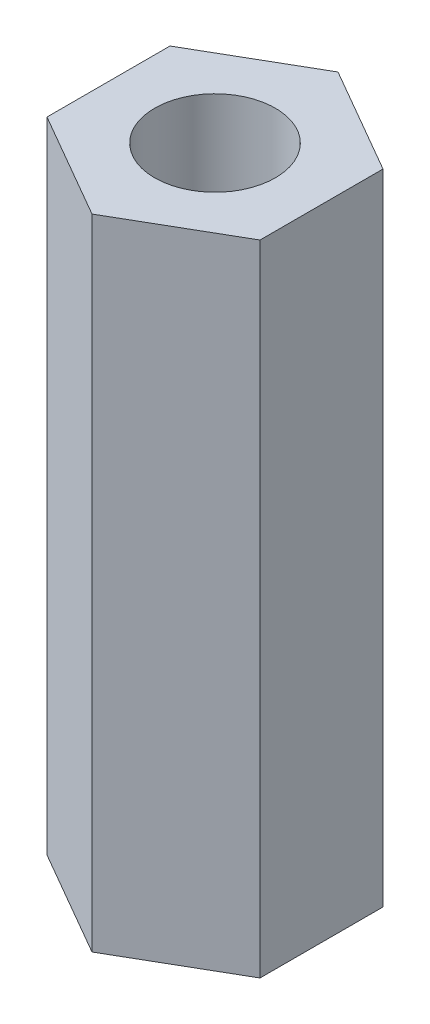
SolidWorks part; units mm, degrees
ref_plane "Front Plane" through (0, 0, 0) normal (0, 0, 1) x (1, 0, 0)
ref_plane "Top Plane" through (0, 0, 0) normal (0, 1, 0) x (1, 0, 0)
ref_plane "Right Plane" through (0, 0, 0) normal (1, 0, 0) x (0, 0, -1)
sketch "Sketch1" plane through (0, 0, 0) normal (0, 1, 0) x (1, 0, 0)
  line L1 (0, -1.7321) -> (1.5, -0.866)
  line L2 (1.5, -0.866) -> (1.5, 0.866)
  line L3 (1.5, 0.866) -> (0, 1.7321)
  line L4 (0, 1.7321) -> (-1.5, 0.866)
  line L5 (-1.5, 0.866) -> (-1.5, -0.866)
  line L6 (-1.5, -0.866) -> (0, -1.7321)
  circle A0 centre (0, 0) radius 1.5 construction
  circle A1 centre (0, 0) radius 0.85
  dimension "D2" = 1.7
  dimension "D1" = 3
extrude "Boss-Extrude1" add sketch "Sketch1" along normal blind 9
